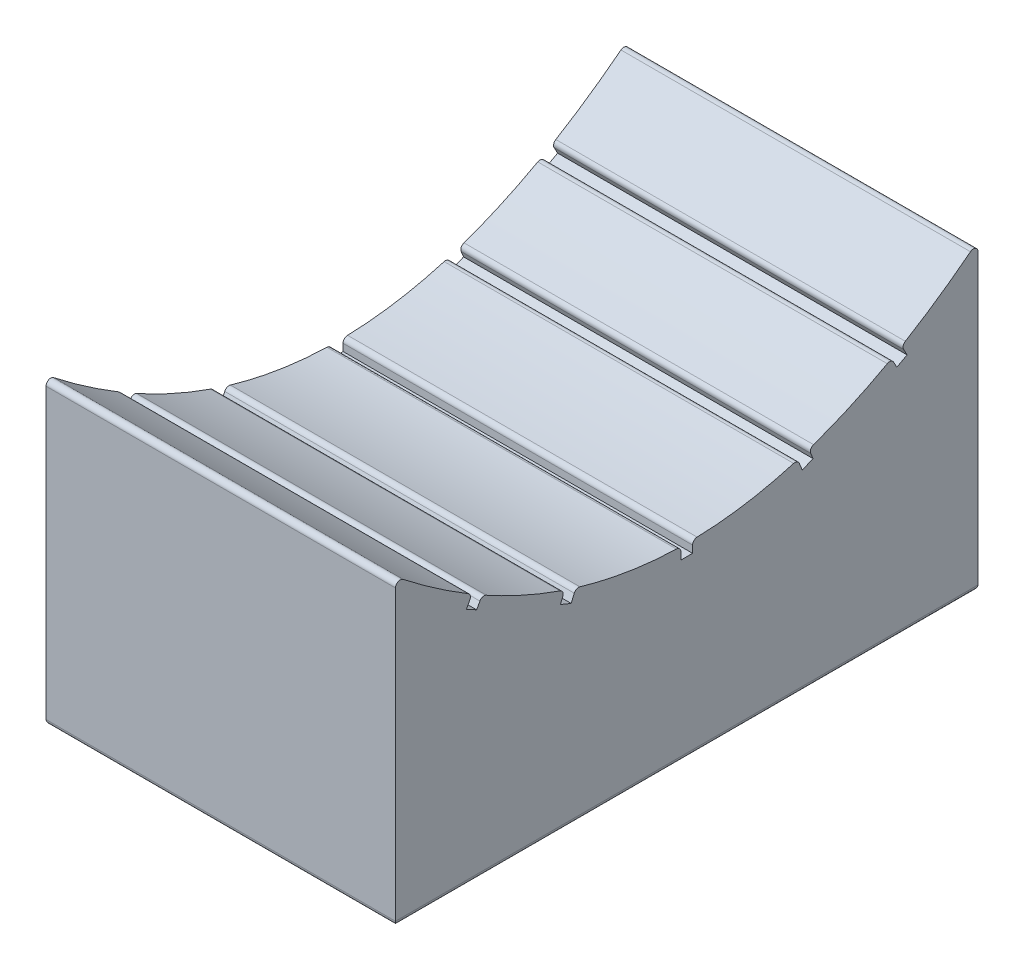
SolidWorks part; units mm, degrees
ref_plane "Front Plane" through (0, 0, 0) normal (0, 0, 1) x (1, 0, 0)
ref_plane "Top Plane" through (0, 0, 0) normal (0, 1, 0) x (1, 0, 0)
ref_plane "Right Plane" through (0, 0, 0) normal (1, 0, 0) x (0, 0, -1)
sketch "Sketch1" plane through (0, 0, 0) normal (1, 0, 0) x (0, 0, -1)
  line L0 (0, 0) -> (25, 0)
  line L1 (25, 0) -> (25, 13)
  line L2 (0, 0) -> (0, 13)
  line L3 (12.5, 8) -> (12.5, 0) construction
  spline S0 degree 2 poles (0, 13) (12.5, 3) (25, 13) knots 0 0 0 1 1 1
  dimension "D1" = 25
  dimension "D2" = 13
  dimension "D3" = 13
  dimension "D4" = 8
extrude "Boss-Extrude1" add sketch "Sketch1" along normal blind 15
sketch "Sketch2" plane through (0, 0, 0) normal (0, -1, 0) x (1, 0, 0)
  line L0 (7.5, 0) -> (7.5, -25) construction
  line L1 (15, 0) -> (0, 0) construction
  line L2 (15, -25) -> (0, -25) construction
  line L4 (6.9, -14.5) -> (8.1, -14.5)
  line L5 (6.9, -14.5) -> (6.9, -10.5)
  line L6 (6.9, -10.5) -> (8.1, -10.5)
  line L7 (8.1, -14.5) -> (8.1, -10.5)
  line L8 (6.9, -14.5) -> (8.1, -10.5) construction
  line L9 (6.9, -10.5) -> (8.1, -14.5) construction
  point P6 (7.5, -12.5)
  dimension "D1" = 1.2
  dimension "D2" = 4
extrude "Cut-Extrude1" cut sketch "Sketch2" against normal blind 7
sketch "Sketch3" plane through (15, 0, 0) normal (1, 0, 0) x (0, 0, -1)
  line L0 (12.5, 8) -> (12.5, 11.2707) construction
  line L1 (7.5, 8.8) -> (7.6904, 9.2623) construction
  line L2 (3.5, 10.592) -> (3.7371, 11.0322) construction
  line L3 (3.0428, 10.2704) -> (3.517, 11.1508)
  line L4 (3.0428, 10.2704) -> (3.483, 10.0332)
  line L5 (3.517, 11.1508) -> (3.9572, 10.9136)
  line L6 (3.483, 10.0332) -> (3.9572, 10.9136)
  line L7 (3.0428, 10.2704) -> (3.9572, 10.9136) construction
  line L8 (3.517, 11.1508) -> (3.483, 10.0332) construction
  line L9 (7.0785, 8.4328) -> (7.4592, 9.3575)
  line L10 (7.0785, 8.4328) -> (7.5408, 8.2425)
  line L11 (7.4592, 9.3575) -> (7.9215, 9.1672)
  line L12 (7.5408, 8.2425) -> (7.9215, 9.1672)
  line L13 (7.0785, 8.4328) -> (7.9215, 9.1672) construction
  line L14 (7.4592, 9.3575) -> (7.5408, 8.2425) construction
  line L15 (12.25, 7.5) -> (12.25, 8.5)
  line L16 (12.25, 7.5) -> (12.75, 7.5)
  line L17 (12.25, 8.5) -> (12.75, 8.5)
  line L18 (12.75, 7.5) -> (12.75, 8.5)
  line L19 (12.25, 7.5) -> (12.75, 8.5) construction
  line L20 (12.25, 8.5) -> (12.75, 7.5) construction
  line L21 (12.5, 0) -> (12.5, 16.8613) construction
  line L22 (0, 0) -> (25, 0) construction
  line L23 (17.5408, 9.3575) -> (17.4592, 8.2425) construction
  line L24 (17.9215, 8.4328) -> (17.0785, 9.1672) construction
  line L25 (21.483, 11.1508) -> (21.517, 10.0332) construction
  line L26 (21.9572, 10.2704) -> (21.0428, 10.9136) construction
  line L27 (21.5, 10.592) -> (21.2629, 11.0322) construction
  line L28 (17.5, 8.8) -> (17.3096, 9.2623) construction
  line L29 (17.4592, 8.2425) -> (17.0785, 9.1672)
  line L30 (17.5408, 9.3575) -> (17.0785, 9.1672)
  line L31 (17.9215, 8.4328) -> (17.4592, 8.2425)
  line L32 (17.9215, 8.4328) -> (17.5408, 9.3575)
  line L33 (21.517, 10.0332) -> (21.0428, 10.9136)
  line L34 (21.483, 11.1508) -> (21.0428, 10.9136)
  line L35 (21.9572, 10.2704) -> (21.517, 10.0332)
  line L36 (21.9572, 10.2704) -> (21.483, 11.1508)
  dimension "D1" = 0.5
  dimension "D2" = 0.5
  dimension "D3" = 0.5
  dimension "D5" = 4
  dimension "D6" = 1
  dimension "D7" = 1
  dimension "D8" = 1
extrude "Cut-Extrude2" cut sketch "Sketch3" against normal blind 37
fillet "Fillet1" radius 0.2 20 edges at (7.5, 0, 0) (15, 0, -12.5) (7.5, 0, -25) (0, 0, -12.5) (6.9, 0, -12.5) (7.5, 0, -14.5) (8.1, 0, -12.5) (7.5, 0, -10.5) (7.5, 13, 0) (7.5, 13, -25) (7.5, 10.718, -3.2839) (7.5, 10.4683, -3.7173) (7.5, 8.878, -7.2618) (7.5, 8.7252, -7.7396) (7.5, 8.002, -12.25) (7.5, 8.002, -12.75) (7.5, 8.7252, -17.2604) (7.5, 8.878, -17.7382) (7.5, 10.4683, -21.2827) (7.5, 10.718, -21.7161)
